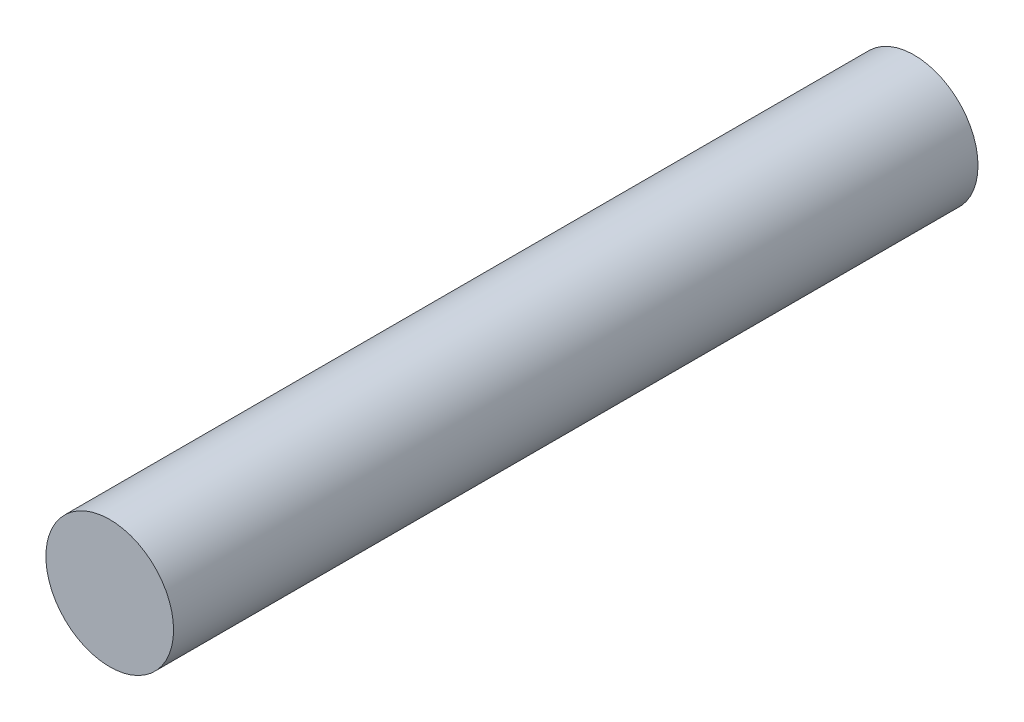
SolidWorks part; units mm, degrees
ref_plane "Plan de face" through (0, 0, 0) normal (0, 0, 1) x (1, 0, 0)
ref_plane "Plan de dessus" through (0, 0, 0) normal (0, 1, 0) x (1, 0, 0)
ref_plane "Plan de droite" through (0, 0, 0) normal (1, 0, 0) x (0, 0, -1)
sketch "Sketch1" plane through (0, 0, 0) normal (0, 0, 1) x (1, 0, 0)
  circle A0 centre (0, 0) radius 2.5
  dimension "D1" = 5
extrude "Boss-Extrude1" add sketch "Sketch1" along normal blind 31.5
